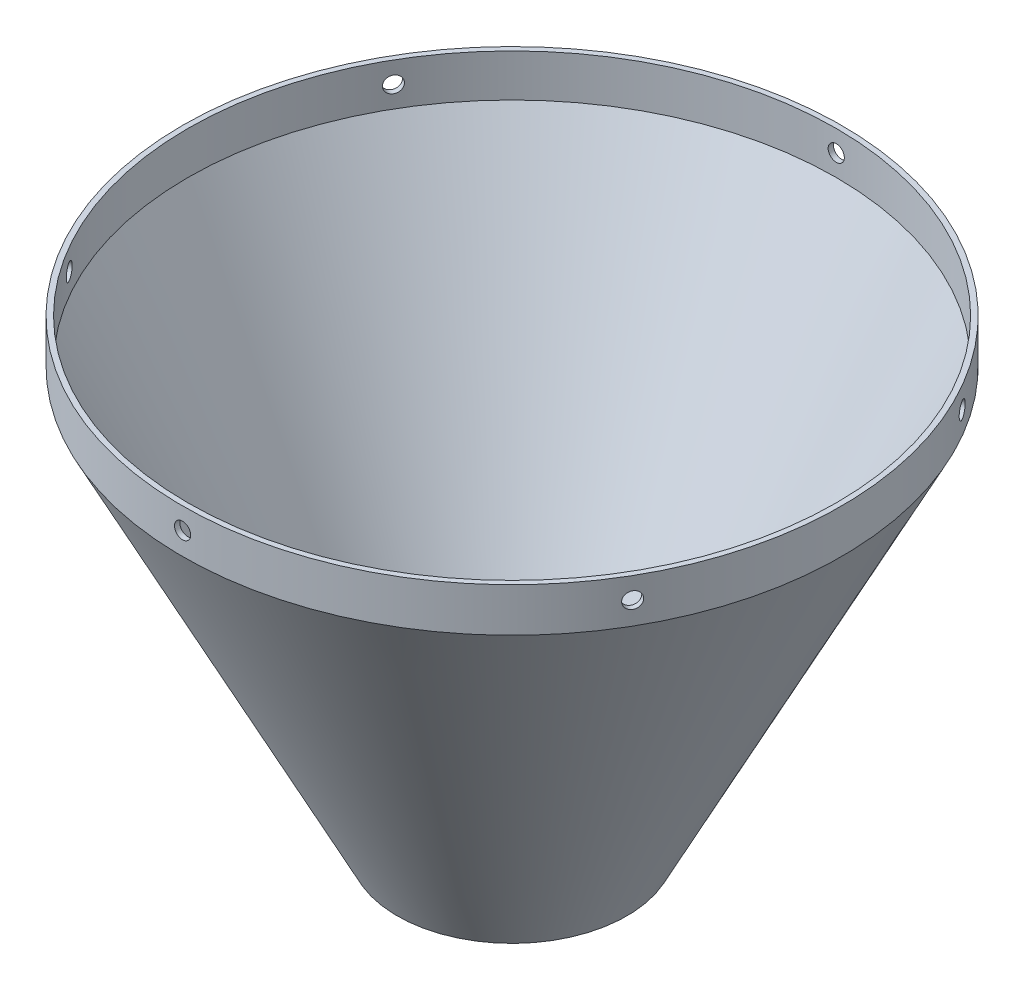
SolidWorks part; units mm, degrees
material "A-Glass Fiber"
ref_plane "Front Plane" through (0, 0, 0) normal (0, 0, 1) x (1, 0, 0)
ref_plane "Top Plane" through (0, 0, 0) normal (0, 1, 0) x (1, 0, 0)
ref_plane "Right Plane" through (0, 0, 0) normal (1, 0, 0) x (0, 0, -1)
sketch "Sketch1" plane through (0, 0, 0) normal (0, 0, 1) x (1, 0, 0)
  line L0 (0, 0) -> (0, 12.7) construction
  line L3 (0, 12.7) -> (96.8375, 12.7) construction
  line L4 (96.8375, 0) -> (96.8375, 12.7)
  line L7 (0, 0) -> (0, -123.825) construction
  line L8 (0, -123.825) -> (33.3375, -123.825) construction
  line L10 (33.3375, -123.825) -> (96.8375, 0)
  line L11 (34.3075, -125.4125) -> (98.425, -0.3833)
  line L12 (98.425, -0.3833) -> (98.425, 12.7)
  line L13 (-1.5875, 14.2875) -> (98.425, 14.2875) construction
  line L14 (-1.5875, 0) -> (-1.5875, 14.2875) construction
  line L15 (-1.5875, 0) -> (-1.5875, -125.4125) construction
  line L16 (-1.5875, -125.4125) -> (34.3075, -125.4125) construction
  line L17 (96.8375, 12.7) -> (98.425, 12.7)
  line L18 (33.3375, -123.825) -> (33.3375, -125.4125)
  line L19 (33.3375, -125.4125) -> (34.3075, -125.4125)
  line L20 (98.425, -0.3833) -> (98.425, 14.2875) construction
  point P0 (0, 0)
  dimension "D1" = 96.8375
  dimension "D2" = 12.7
  dimension "D3" = 1.5875
  dimension "D4" = 123.825
  dimension "D5" = 33.3375
revolve "Revolve1" add sketch "Sketch1" angle 360 about L7
sketch "Sketch2" plane through (0, 0, 0) normal (0, 0, 1) x (1, 0, 0)
  line L0 (0, 0) -> (0, 12.7) construction
  line L1 (98.425, 12.7) -> (-98.425, 12.7) construction
  circle A0 centre (0, 6.35) radius 2.413
  dimension "D1" = 4.826
extrude "Cut-Extrude1" cut sketch "Sketch2" against normal through all both and the other way through all
pattern_circular "CirPattern1" count 6 over 360 about axis through (0, 12.7, 0) along (0, 1, 0) of "Cut-Extrude1"
